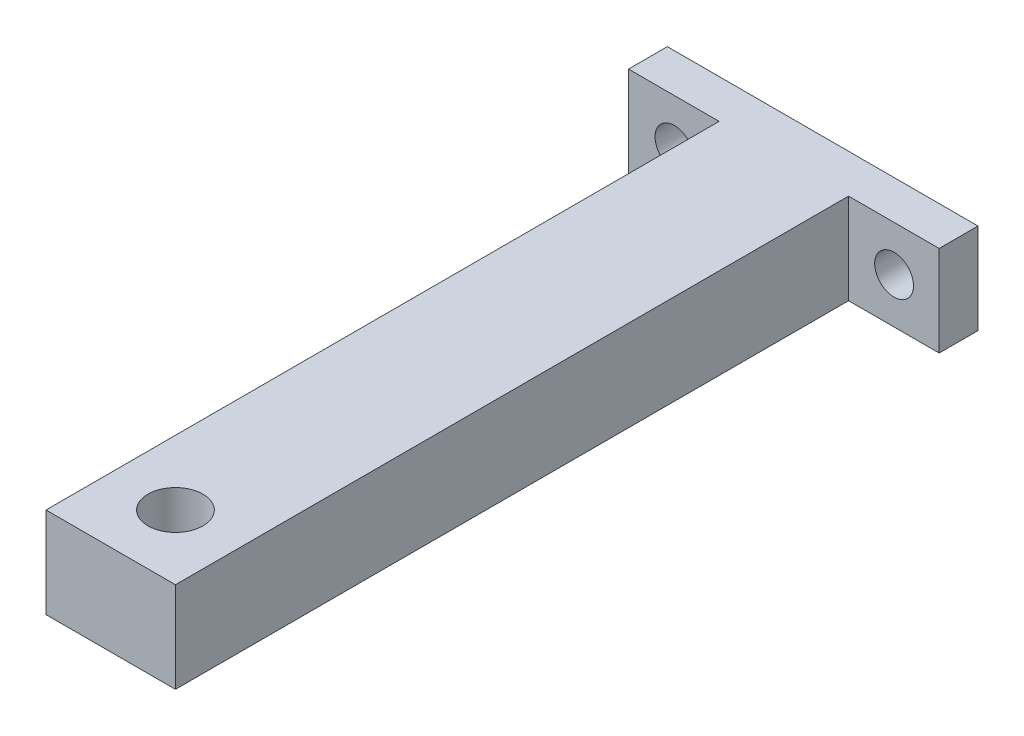
SolidWorks part; units mm, degrees
ref_plane "Front" through (0, 0, 0) normal (0, 0, 1) x (1, 0, 0)
ref_plane "Top" through (0, 0, 0) normal (0, 1, 0) x (1, 0, 0)
ref_plane "Right" through (0, 0, 0) normal (1, 0, 0) x (0, 0, -1)
sketch "Эскиз1" plane through (0, 0, 0) normal (0, 0, 1) x (1, 0, 0)
  line L1 (-12, 3.5) -> (12, 3.5)
  line L2 (-12, 3.5) -> (-12, -3.5)
  line L3 (-12, -3.5) -> (12, -3.5)
  line L4 (12, 3.5) -> (12, -3.5)
  line L5 (-12, 3.5) -> (12, -3.5) construction
  line L6 (-12, -3.5) -> (12, 3.5) construction
  point P0 (0, 0)
  dimension "D1" = 7
  dimension "D2" = 24
extrude "Бобышка-Вытянуть2" add sketch "Эскиз1" along normal blind 3
sketch "Эскиз3" plane through (0, 0, 3) normal (0, 0, 1) x (1, 0, 0)
  line L0 (12, 3.5) -> (-12, 3.5) construction
  line L1 (-5, 3.5) -> (5, 3.5)
  line L2 (-5, 3.5) -> (-5, -3.5)
  line L3 (-5, -3.5) -> (5, -3.5)
  line L4 (5, 3.5) -> (5, -3.5)
  line L5 (-12, -3.5) -> (12, -3.5) construction
  line L6 (-12, 3.5) -> (-12, -3.5) construction
  line L7 (12, -3.5) -> (12, 3.5) construction
  dimension "D1" = 7
  dimension "D2" = 7
extrude "Бобышка-Вытянуть4" add sketch "Эскиз3" along normal blind 52
sketch "Эскиз5" plane through (0, -3.5, 0) normal (0, -1, 0) x (-1, 0, 0)
  line L0 (12, 0) -> (-12, 0) construction
  circle A0 centre (0, -50) radius 2.125
  dimension "D1" = 4.25
  dimension "D2" = 50
extrude "Вырез-Вытянуть1" cut sketch "Эскиз5" against normal blind 7
sketch "Эскиз6" plane through (0, 0, 3) normal (0, 0, 1) x (1, 0, 0)
  circle A0 centre (8.5165, 0) radius 1.5
  dimension "D1" = 3
extrude "Вырез-Вытянуть2" cut sketch "Эскиз6" against normal blind 3
sketch "Эскиз7" plane through (0, 0, 3) normal (0, 0, 1) x (1, 0, 0)
  circle A0 centre (-8.4523, 0) radius 1.5
  dimension "D1" = 3
extrude "Вырез-Вытянуть3" cut sketch "Эскиз7" against normal blind 3
